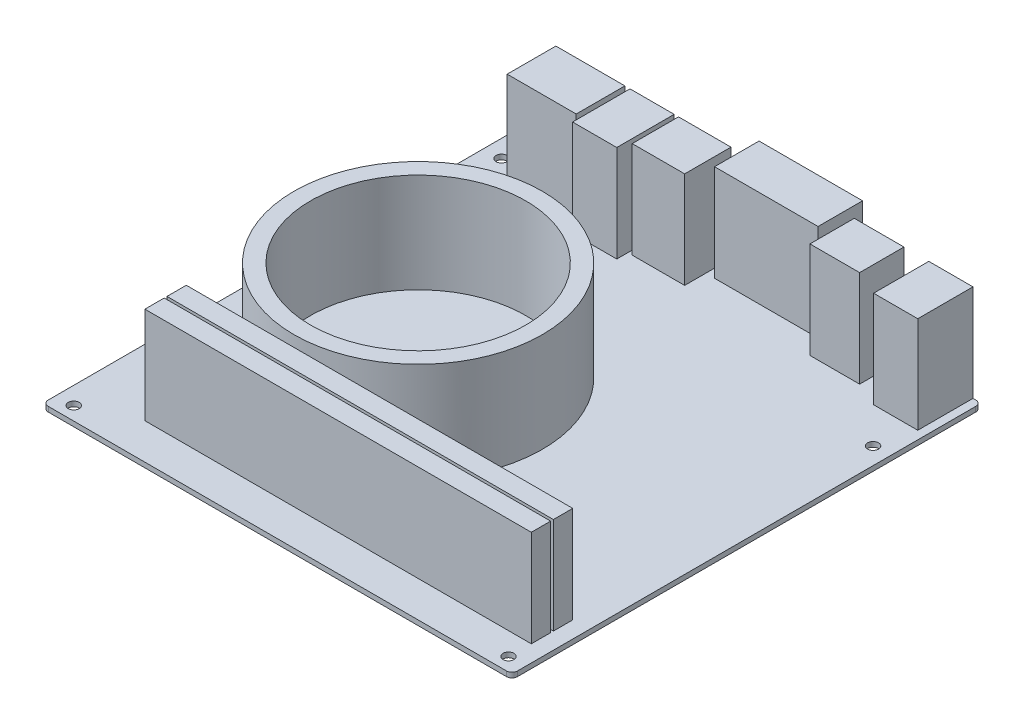
SolidWorks part; units mm, degrees
material "Silicon"
ref_plane "Front Plane" through (0, 0, 0) normal (0, 0, 1) x (1, 0, 0)
ref_plane "Top Plane" through (0, 0, 0) normal (0, 1, 0) x (1, 0, 0)
ref_plane "Right Plane" through (0, 0, 0) normal (1, 0, 0) x (0, 0, -1)
sketch "Sketch1" plane through (0, 0, 0) normal (0, 1, 0) x (1, 0, 0)
  line L0 (0, -85) -> (0, 85) construction
  line L1 (-85, -85) -> (85, -85)
  line L2 (-85, -85) -> (-85, 85)
  line L3 (-85, 85) -> (85, 85)
  line L4 (85, -85) -> (85, 85)
  line L5 (-85, 0) -> (85, 0) construction
  dimension "D1" = 170
extrude "Boss-Extrude1" add sketch "Sketch1" along normal blind 1.8
fillet "Fillet1" radius 2 4 edges at (-85, 0.9, 85) (-85, 0.9, -85) (85, 0.9, -85) (85, 0.9, 85)
sketch "Sketch2" plane through (0, 1.8, 0) normal (0, 1, 0) x (1, 0, 0)
  line L1 (-78.65, 74.84) -> (78.83, 74.84) construction
  line L2 (-78.65, 74.84) -> (-78.65, -80.1) construction
  line L3 (-78.65, -80.1) -> (78.83, -80.1) construction
  line L4 (78.83, 74.84) -> (78.83, 51.98) construction
  line L5 (-85, 83) -> (-85, -83) construction
  line L6 (83, 85) -> (-83, 85) construction
  line L7 (78.83, 51.98) -> (78.83, -80.1) construction
  circle A0 centre (-78.65, 74.84) radius 1.98
  circle A1 centre (-78.65, -80.1) radius 1.98
  circle A2 centre (78.83, -80.1) radius 1.98
  circle A3 centre (78.83, 51.98) radius 1.98
  dimension "D6" = 3.96
  dimension "D1" = 157.48
  dimension "D2" = 154.94
  dimension "D3" = 6.35
  dimension "D4" = 10.16
  dimension "D5" = 22.86
extrude "Cut-Extrude1" cut sketch "Sketch2" against normal blind 2
sketch "Sketch3" plane through (0, 1.8, 0) normal (0, 1, 0) x (1, 0, 0)
  line L0 (83, 85) -> (-83, 85) construction
  line L1 (82, 85) -> (66, 85)
  line L2 (82, 85) -> (82, 65)
  line L3 (82, 65) -> (66, 65)
  line L4 (66, 85) -> (66, 65)
  line L5 (35, 92) -> (-2.5, 92)
  line L6 (57, 85) -> (39, 85)
  line L7 (57, 85) -> (57, 68.9389)
  line L8 (57, 68.9389) -> (39, 68.9389)
  line L9 (39, 85) -> (39, 68.9389)
  line L10 (85, -83) -> (85, 83) construction
  line L11 (35, 92) -> (35, 75.878)
  line L12 (35, 75.878) -> (-2.5, 75.878)
  line L13 (-2.5, 92) -> (-2.5, 75.878)
  line L14 (-5.6721, 85) -> (-24.6721, 85)
  line L15 (-5.6721, 85) -> (-5.6721, 68.2198)
  line L16 (-5.6721, 68.2198) -> (-24.6721, 68.2198)
  line L17 (-24.6721, 85) -> (-24.6721, 68.2198)
  line L18 (-26.2446, 85) -> (-42.2446, 85)
  line L19 (-26.2446, 85) -> (-26.2446, 64.1984)
  line L20 (-26.2446, 64.1984) -> (-42.2446, 64.1984)
  line L21 (-42.2446, 85) -> (-42.2446, 64.1984)
  line L22 (-44.1032, 85) -> (-69.1032, 85)
  line L23 (-44.1032, 85) -> (-44.1032, 67.3581)
  line L24 (-44.1032, 67.3581) -> (-69.1032, 67.3581)
  line L25 (-69.1032, 85) -> (-69.1032, 67.3581)
  dimension "D1" = 7
  dimension "D2" = 50
  dimension "D3" = 37.5
  dimension "D4" = 16
  dimension "D5" = 3
  dimension "D6" = 28
  dimension "D7" = 18
  dimension "D8" = 19
  dimension "D9" = 16
  dimension "D10" = 25
  dimension "D11" = 20
extrude "Boss-Extrude2" add sketch "Sketch3" along normal blind 35
sketch "Sketch4" plane through (0, 1.8, 0) normal (0, 1, 0) x (1, 0, 0)
  line L0 (85, -83) -> (85, 83) construction
  line L1 (79, -72) -> (-61, -72)
  line L2 (79, -72) -> (79, -65)
  line L3 (79, -65) -> (-61, -65)
  line L4 (-61, -72) -> (-61, -65)
  line L5 (-83, -85) -> (83, -85) construction
  dimension "D1" = 6
  dimension "D2" = 13
  dimension "D3" = 7
  dimension "D4" = 140
extrude "Boss-Extrude3" add sketch "Sketch4" along normal blind 35
pattern_linear "LPattern1" count 2 spacing 8 along (0, 0, -1) of "Boss-Extrude3"
sketch "Sketch5" plane through (0, 1.8, 0) normal (0, 1, 0) x (1, 0, 0)
  line L0 (-85, 83) -> (-85, -83) construction
  line L1 (-83, -85) -> (83, -85) construction
  circle A0 centre (-25, -9) radius 45
  circle A1 centre (-25, -9) radius 39
  dimension "D3" = 90
  dimension "D4" = 78
  dimension "D1" = 60
  dimension "D2" = 76
extrude "Boss-Extrude4" add sketch "Sketch5" along normal blind 36
